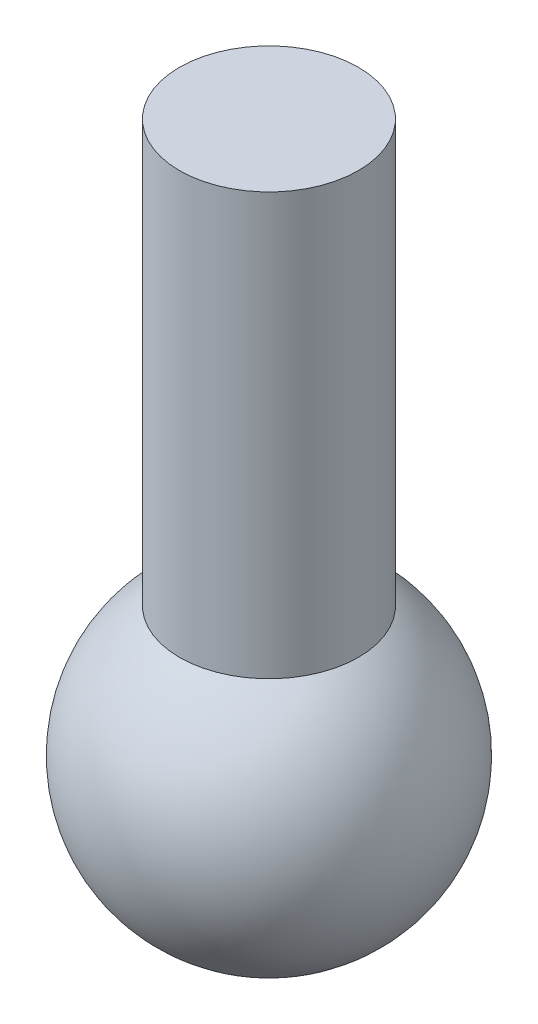
SolidWorks part; units mm, degrees
ref_plane "정면" through (0, 0, 0) normal (0, 0, 1) x (1, 0, 0)
ref_plane "윗면" through (0, 0, 0) normal (0, 1, 0) x (1, 0, 0)
ref_plane "우측면" through (0, 0, 0) normal (1, 0, 0) x (0, 0, -1)
sketch "스케치1" plane through (0, 0, 0) normal (0, 1, 0) x (1, 0, 0)
  line L0 (0, 3.6106) -> (0, -4.3389) construction
  line L1 (0, 2.2) -> (0, -2.2)
  arc A0 (0, -2.2) -> (0, 2.2) centre (0, 0) ccw
  dimension "D1" = 4.4
revolve "회전6" add sketch "스케치1" angle 360 about L0
ref_plane "평면1" through (0, 7.7, 0) normal (0, 1, 0) x (1, 0, 0)
sketch "스케치3" plane through (0, 7.7, 0) normal (0, 1, 0) x (1, 0, 0)
  circle A0 centre (0, 0) radius 1.25
  dimension "D1" = 2.5
extrude "보스-돌출2" add sketch "스케치3" against normal up to surface (5.8896 mm away)
